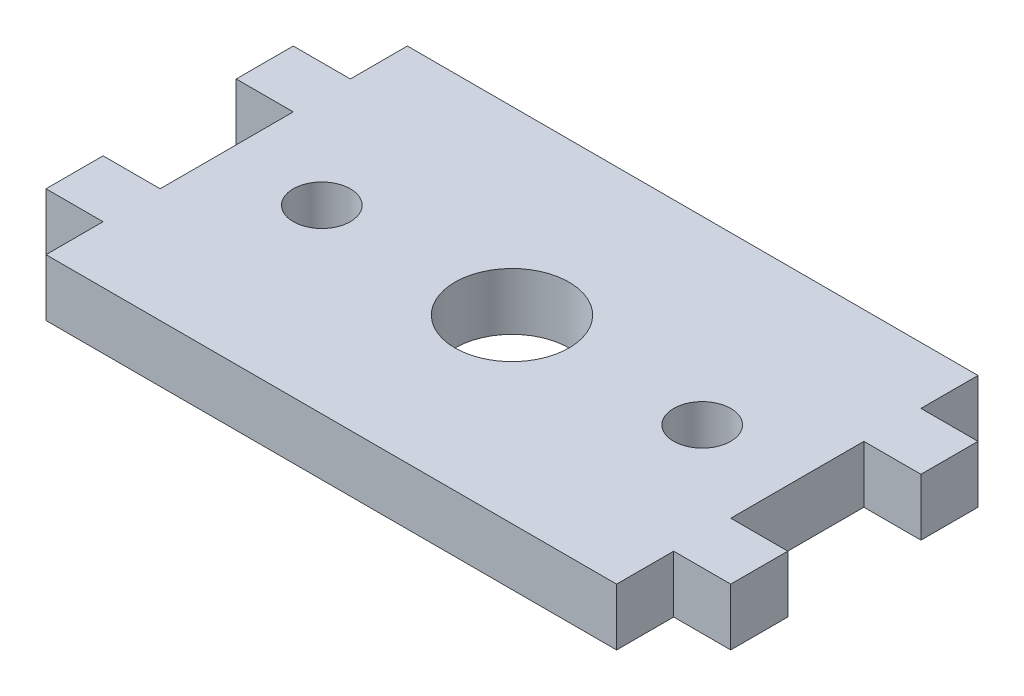
SolidWorks part; units mm, degrees
ref_plane "Front Plane" through (0, 0, 0) normal (0, 0, 1) x (1, 0, 0)
ref_plane "Top Plane" through (0, 0, 0) normal (0, 1, 0) x (1, 0, 0)
ref_plane "Right Plane" through (0, 0, 0) normal (1, 0, 0) x (0, 0, -1)
sketch "Sketch1" plane through (0, 0, 0) normal (0, 1, 0) x (1, 0, 0)
  line L0 (-42.8674, 7) -> (-42.8674, 10)
  line L1 (-42.8674, 10) -> (-39.8674, 10)
  line L2 (-39.8674, 10) -> (-39.8674, 13)
  line L3 (-39.8674, 13) -> (-9.8674, 13)
  line L4 (-9.8674, 13) -> (-9.8674, 10)
  line L5 (-9.8674, 10) -> (-6.8674, 10)
  line L6 (-6.8674, 10) -> (-6.8674, 7)
  line L7 (-6.8674, 7) -> (-9.8674, 7)
  line L8 (-9.8674, 7) -> (-9.8674, 0)
  line L9 (-9.8674, 0) -> (-6.8674, 0)
  line L10 (-6.8674, 0) -> (-6.8674, -3)
  line L11 (-6.8674, -3) -> (-9.8674, -3)
  line L12 (-9.8674, -3) -> (-9.8674, -6)
  line L13 (-9.8674, -6) -> (-39.8674, -6)
  line L14 (-39.8674, -6) -> (-39.8674, -3)
  line L15 (-39.8674, -3) -> (-42.8674, -3)
  line L16 (-42.8674, -3) -> (-42.8674, 0)
  line L17 (-42.8674, 0) -> (-39.8674, 0)
  line L18 (-39.8674, 0) -> (-39.8674, 7)
  line L19 (-39.8674, 7) -> (-42.8674, 7)
  line L20 (-24.8674, 13) -> (-24.8674, 3.5) construction
  line L21 (-24.8674, 3.5) -> (-34.8674, 3.5) construction
  circle A0 centre (-24.8674, 3.5) radius 3
  circle A1 centre (-34.8674, 3.5) radius 1.5
  circle A2 centre (-14.8674, 3.5) radius 1.5
  dimension "D6" = 10
  dimension "D7" = 3
  dimension "D1" = 3
  dimension "D2" = 3
  dimension "D3" = 30
  dimension "D4" = 7
  dimension "D5" = 3
extrude "Boss-Extrude1" add sketch "Sketch1" along normal blind 3
